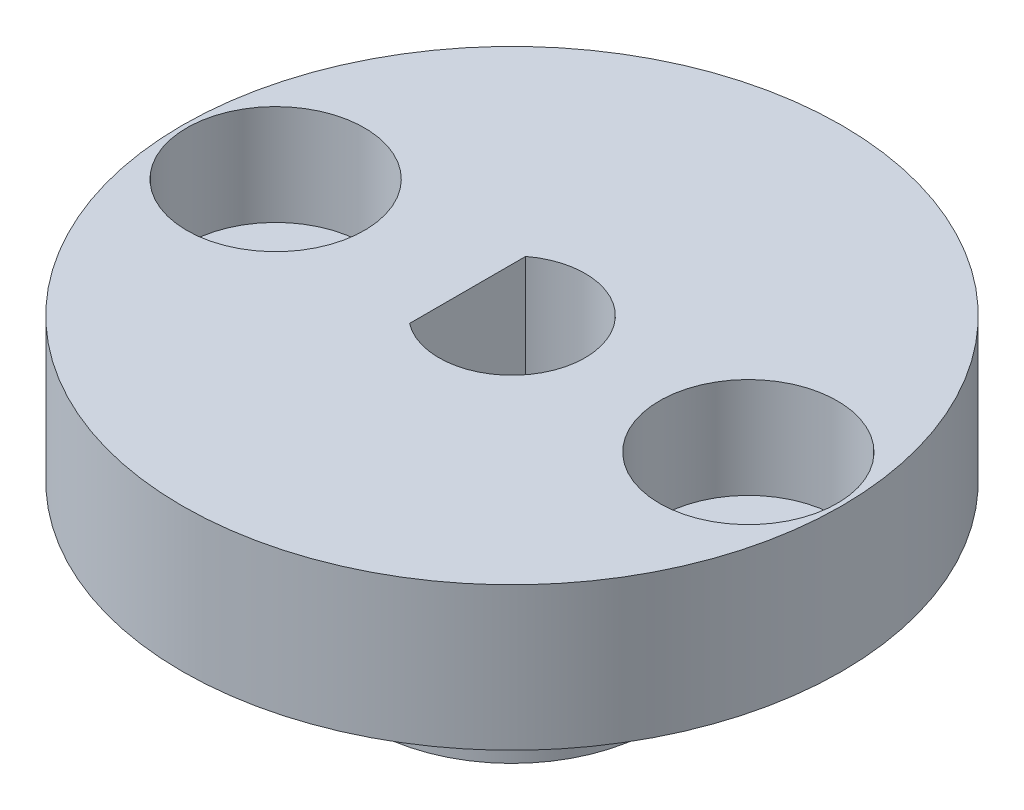
SolidWorks part; units mm, degrees
ref_plane "Alzado" through (0, 0, 0) normal (0, 0, 1) x (1, 0, 0)
ref_plane "Planta" through (0, 0, 0) normal (0, 1, 0) x (1, 0, 0)
ref_plane "Vista lateral" through (0, 0, 0) normal (1, 0, 0) x (0, 0, -1)
sketch "Croquis1" plane through (0, 0, 0) normal (0, 1, 0) x (1, 0, 0)
  circle A0 centre (0, 0) radius 11.5
  dimension "D1" = 23
extrude "Saliente-Extruir1" add sketch "Croquis1" along normal blind 5
sketch "Croquis2" plane through (0, 0, 0) normal (0, -1, 0) x (1, 0, 0)
  circle A0 centre (0, 0) radius 4.99
  dimension "D1" = 9.98
extrude "Saliente-Extruir2" add sketch "Croquis2" along normal blind 5
sketch "Croquis3" plane through (0, 0, 0) normal (0, -1, 0) x (1, 0, 0)
  line L0 (0, 0) -> (0, 5.9276) construction
  line L1 (-4.99, 0) -> (-11.5, 0) construction
  circle A0 centre (-8.245, 0) radius 1.6
  circle A1 centre (8.245, 0) radius 1.6
  circle A2 centre (0, 0) radius 4.99 construction
  circle A3 centre (0, 0) radius 4.99 construction
  circle A4 centre (0, 0) radius 11.5 construction
  dimension "D1" = 3.2
extrude "Cortar-Extruir1" cut sketch "Croquis3" against normal through all
sketch "Croquis4" plane through (0, -5, 0) normal (0, -1, 0) x (1, 0, 0)
  line L0 (-1.55, 2.0248) -> (-1.55, -2.0248)
  arc A0 (-1.55, -2.0248) -> (-1.55, 2.0248) centre (0, 0) ccw
  dimension "D1" = 5.1
  dimension "D2" = 4.1
extrude "Cortar-Extruir2" cut sketch "Croquis4" against normal through all
sketch "Croquis5" plane through (0, 5, 0) normal (0, 1, 0) x (1, 0, 0)
  circle A0 centre (-8.245, 0) radius 3.1
  circle A1 centre (8.245, 0) radius 3.1
  dimension "D1" = 6.2
extrude "Cortar-Extruir3" cut sketch "Croquis5" against normal blind 3.5
